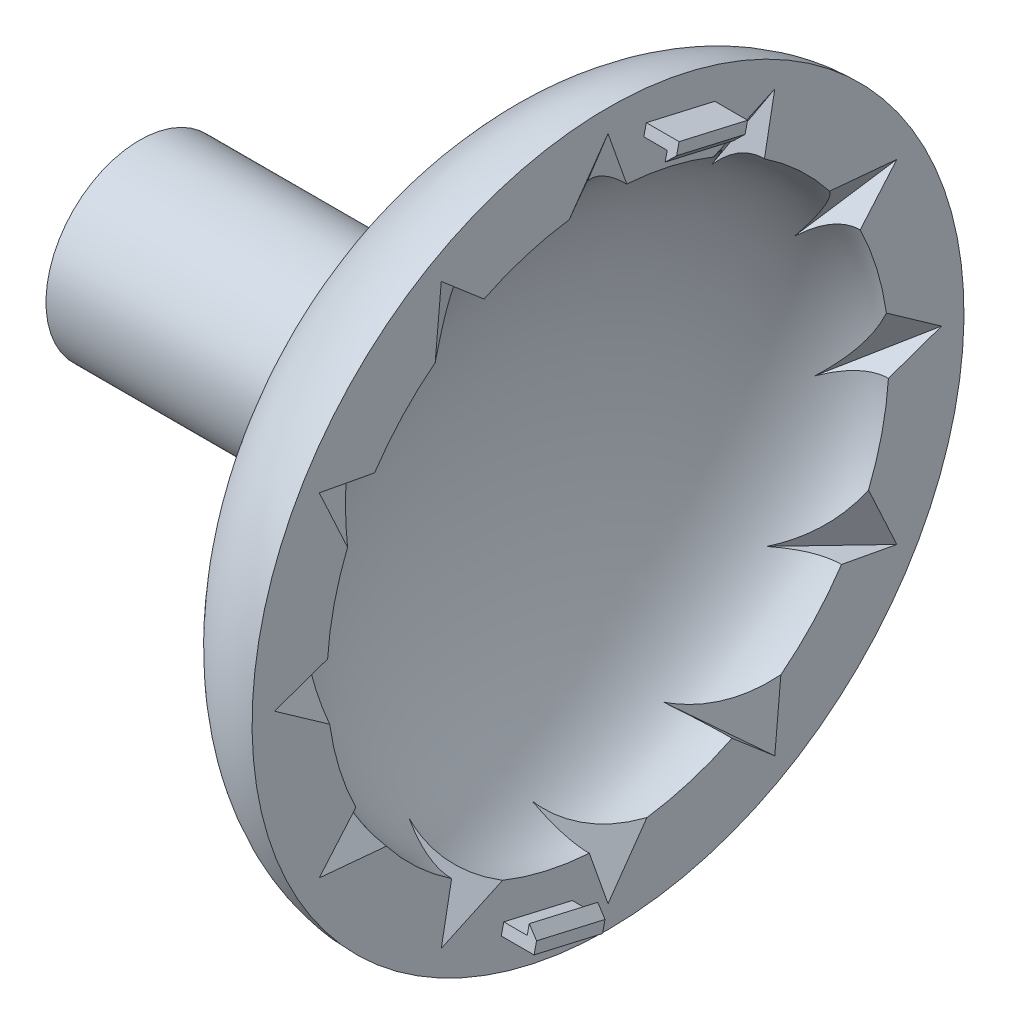
SolidWorks part; units mm, degrees
material "Acrylic (Medium-high impact)"
ref_plane "Front Plane" through (0, 0, 0) normal (0, 0, 1) x (1, 0, 0)
ref_plane "Top Plane" through (0, 0, 0) normal (0, 1, 0) x (1, 0, 0)
ref_plane "Right Plane" through (0, 0, 0) normal (1, 0, 0) x (0, 0, -1)
sketch "Sketch1" plane through (0, 0, 0) normal (0, 0, 1) x (1, 0, 0)
  line L0 (0, -48.26) -> (0, -38.1)
  line L1 (0, 38.1) -> (0, 48.26)
  line L2 (0, 0) -> (0, 48.26) construction
  line L3 (-26.035, 0) -> (-15.875, 0)
  ellipse E0 centre (0, 0) end of major axis (0, -38.1) minor radius 15.875 (0, 38.1) -> (0, -38.1) ccw
  ellipse E1 centre (0, 0) end of major axis (0, -48.26) minor radius 26.035 (0, 48.26) -> (0, -48.26) ccw
  point P4 (0, 0)
  dimension "D1" = 15.875
  dimension "D2" = 38.1
  dimension "D3" = 26.035
  dimension "D4" = 48.26
revolve "Revolve2" add sketch "Sketch1" angle 360 about L3
ref_plane "Plane1" through (0, -34.29, 0) normal (0, 1, 0) x (1, 0, 0)
ref_plane "Plane2" through (0, -45.212, 0) normal (0, 1, 0) x (1, 0, 0)
sketch "Sketch2" plane through (0, -34.29, 0) normal (0, 1, 0) x (1, 0, 0)
  line L0 (0, -48.26) -> (0, 48.26) construction
  line L1 (0, 7.699) -> (-6.6675, -3.8495)
  line L2 (-6.6675, -3.8495) -> (6.6675, -3.8495)
  line L3 (6.6675, -3.8495) -> (0, 7.699)
  circle A0 centre (0, 0) radius 3.8495 construction
  dimension "D1" = 13.335
sketch "Sketch3" plane through (0, -45.212, 0) normal (0, 1, 0) x (1, 0, 0)
  point P0 (0, 0)
loft "Cut-Loft1" cut profiles "Sketch2", "Sketch3"
pattern_circular "CirPattern1" count 12 over 360 about axis through (0, 0, 0) along (1, 0, 0) of "Cut-Loft1"
sketch "Sketch6" plane through (0, 0, 0) normal (1, 0, 0) x (0, 0, -1)
  line L0 (8.5266, 37.1336) -> (-8.5266, -37.1336) construction
  line L1 (8.5266, 37.1336) -> (10.8004, 47.0359) construction
  line L2 (-8.5266, -37.1336) -> (-10.8004, -47.0359) construction
  line L3 (5.0218, 43.1506) -> (14.3052, 41.019)
  line L4 (4.8512, 42.4079) -> (14.1347, 40.2763)
  line L5 (5.1923, 43.8933) -> (14.4757, 41.7616)
  line L6 (5.1923, 43.8933) -> (4.8512, 42.4079)
  line L7 (14.4757, 41.7616) -> (14.1347, 40.2763)
  line L8 (0, 0) -> (16.9193, -3.885) construction
  arc A0 (14.3014, 35.314) -> (2.5364, 38.0155) centre (0, 0) ccw construction
  arc A1 (-14.3014, -35.314) -> (-2.5364, -38.0155) centre (0, 0) ccw construction
  circle A2 centre (0, 0) radius 48.26 construction
  point P15 (9.6635, 42.0848)
  dimension "D1" = 9.525
  dimension "D2" = 0.762
  dimension "D3" = 0.762
extrude "Boss-Extrude1" add sketch "Sketch6" along normal blind 4.445 contours L4 L7 L5 L6
sketch "Sketch7" plane through (0, 1.0658, 4.6417) normal (0, 0.2238, 0.9746) x (1, 0, 0)
  line L0 (3.175, 42.418) -> (3.175, 41.148)
  line L1 (4.445, 42.418) -> (0, 42.418) construction
  line L2 (3.175, 41.148) -> (4.445, 42.418)
  line L3 (3.175, 42.418) -> (4.445, 42.418)
  dimension "D1" = 1.27
  dimension "D2" = 1.27
extrude "Boss-Extrude2" add sketch "Sketch7" against normal up to surface (9.525 mm away) up to face at (2.2225, 41.019, -14.3052)
ref_plane "Plane3" through (0, 0, 0) normal (0, -0.9746, 0.2238) x (-1, 0, 0)
mirror "Mirror1" about plane through (0, 0, 0) normal (0, -0.9746, 0.2238) of "Boss-Extrude1", "Boss-Extrude2"
ref_plane "Plane4" through (-63.5, 0, 0) normal (1, 0, 0) x (0, 0, -1)
sketch "Sketch8" plane through (-63.5, 0, 0) normal (1, 0, 0) x (0, 0, -1)
  circle A0 centre (0, 0) radius 12.7
  dimension "D1" = 25.4
extrude "Boss-Extrude3" add sketch "Sketch8" along normal up to surface (38.3827 mm away)
